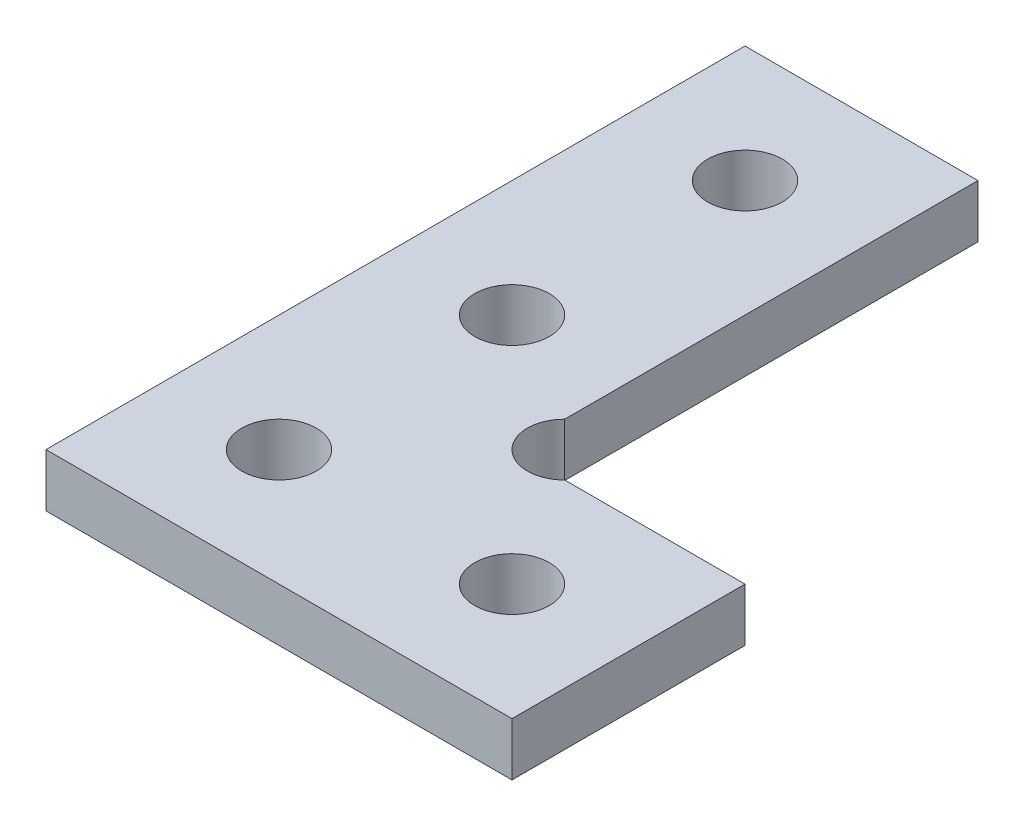
SolidWorks part; units mm, degrees
material "6061-T6 (SS)"
ref_plane "Front Plane" through (0, 0, 0) normal (0, 0, 1) x (1, 0, 0)
ref_plane "Top Plane" through (0, 0, 0) normal (0, 1, 0) x (1, 0, 0)
ref_plane "Right Plane" through (0, 0, 0) normal (1, 0, 0) x (0, 0, -1)
sketch "Sketch1" plane through (0, 0, 2280) normal (0, 1, 0) x (1, 0, 0)
  line L40 (10, 2292.2627) -> (10, 2310)
  line L41 (10, 2310) -> (0, 2310)
  line L42 (0, 2310) -> (0, 2280)
  line L43 (0, 2280) -> (20, 2280)
  line L44 (20, 2280) -> (20, 2290)
  line L45 (20, 2290) -> (12.2627, 2290)
  arc A0 (10, 2292.2627) -> (12.2627, 2290) centre (11.13, 2291.13) ccw
  dimension "D5" = 1.6
  dimension "D1" = 10
  dimension "D2" = 30
  dimension "D3" = 20
  dimension "D4" = 10
  dimension "D6" = 1.13
  dimension "D7" = 1.13
extrude "Boss-Extrude1" add sketch "Sketch1" against normal mid plane 2.28
hole_wizard "Ø3.2 (3.2) Diameter Hole1" positions "Sketch3" profile "Sketch2" hole size "Ø3.2" standard "Ansi Metric"
sketch "Sketch3" plane through (0, 1.14, 0) normal (0, 1, 0) x (1, 0, 0)
  line L0 (5, 30) -> (5, 5) construction
  line L1 (10, 30) -> (0, 30) construction
  line L2 (5, 5) -> (20, 5) construction
  line L4 (20, 0) -> (20, 10) construction
  point P0 (5, 25)
  point P1 (5, 5)
  point P3 (15, 5)
  point P20 (5, 15)
  dimension "D1" = 5
  dimension "D2" = 15
  dimension "D3" = 5
sketch "Sketch2" plane through (5, 1.14, -25) normal (1, 0, 0) x (0, 0, 1)
  line L0 (0, 0) -> (0, 10.9614)
  line L1 (0, 10.9614) -> (1.6, 10)
  line L2 (1.6, 10) -> (1.6, 0)
  line L5 (1.6, 0) -> (0, 0)
  line L10 (0, 10.9614) -> (-1.6, 10) construction
  line L11 (0, -6.35) -> (0, 107.95) construction
  dimension "Hole Dia." = 3.2
  dimension "Hole Depth" = 10
  dimension "Drill Angle" = 118
